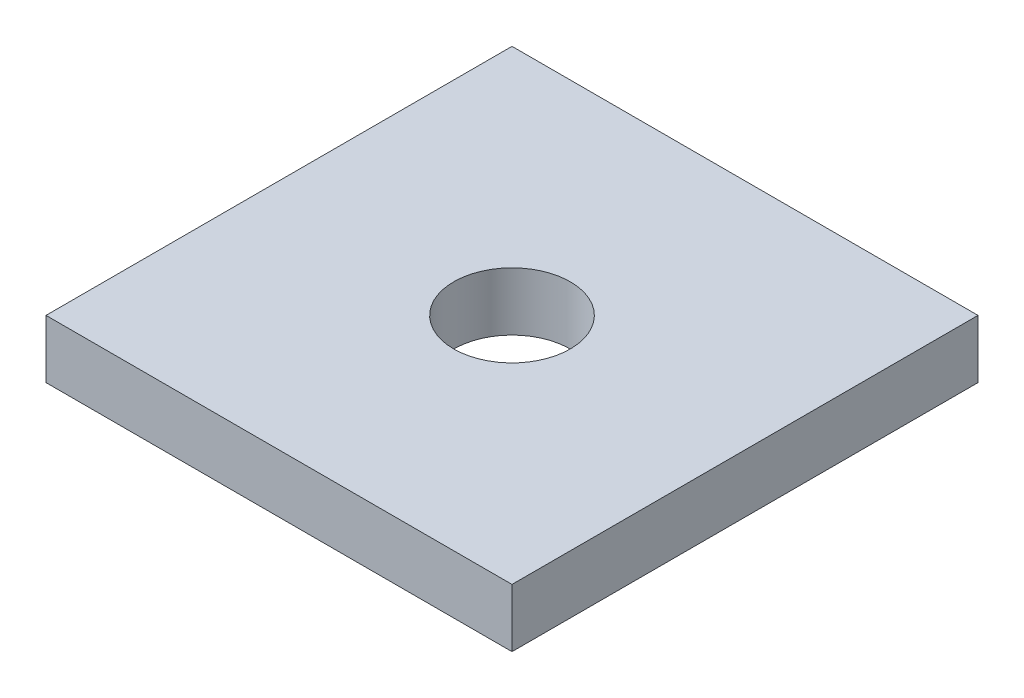
SolidWorks part; units mm, degrees
ref_plane "Front Plane" through (0, 0, 0) normal (0, 0, 1) x (1, 0, 0)
ref_plane "Top Plane" through (0, 0, 0) normal (0, 1, 0) x (1, 0, 0)
ref_plane "Right Plane" through (0, 0, 0) normal (1, 0, 0) x (0, 0, -1)
sketch "Sketch1" plane through (0, 0, 0) normal (0, 1, 0) x (1, 0, 0)
  line L1 (0, 0) -> (76.2, 0)
  line L2 (0, 0) -> (0, 76.2)
  line L3 (0, 76.2) -> (76.2, 76.2)
  line L4 (76.2, 0) -> (76.2, 76.2)
  circle A0 centre (38.1, 38.1) radius 9.525
  dimension "D5" = 19.05
  dimension "D1" = 76.2
  dimension "D2" = 76.2
  dimension "D3" = 38.1
  dimension "D4" = 38.1
extrude "Boss-Extrude1" add sketch "Sketch1" along normal blind 9.525
equation "\"D3@Sketch1\" = \"D1@Sketch1\"/2"
equation "\"D4@Sketch1\" = \"D2@Sketch1\"/2"
